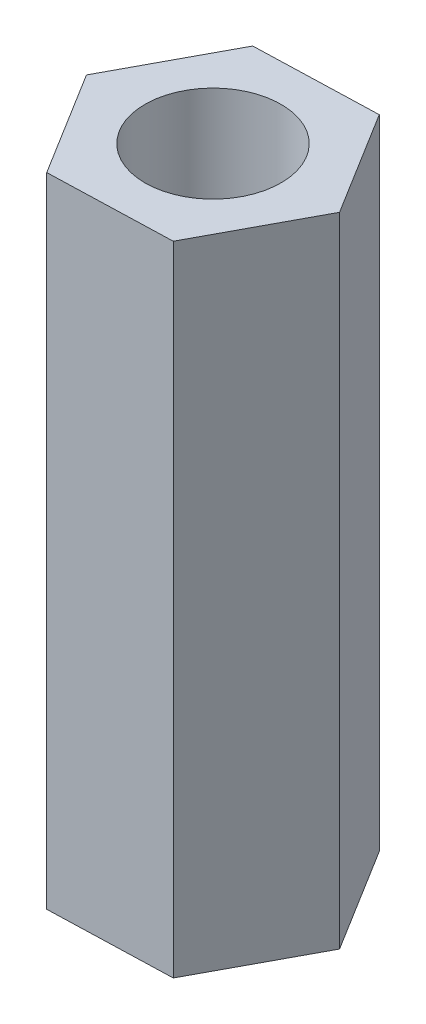
SolidWorks part; units mm, degrees
ref_plane "Front Plane" through (0, 0, 0) normal (0, 0, 1) x (1, 0, 0)
ref_plane "Top Plane" through (0, 0, 0) normal (0, 1, 0) x (1, 0, 0)
ref_plane "Right Plane" through (0, 0, 0) normal (1, 0, 0) x (0, 0, -1)
sketch "Sketch1" plane through (0, 0, 0) normal (0, 1, 0) x (1, 0, 0)
  line L1 (1.3651, 2.5436) -> (-1.5202, 2.454)
  line L2 (-1.5202, 2.454) -> (-2.8854, -0.0895)
  line L3 (-2.8854, -0.0895) -> (-1.3651, -2.5436)
  line L4 (-1.3651, -2.5436) -> (1.5202, -2.454)
  line L5 (1.5202, -2.454) -> (2.8854, 0.0895)
  line L6 (2.8854, 0.0895) -> (1.3651, 2.5436)
  circle A0 centre (0, 0) radius 1.6
  circle A1 centre (0, 0) radius 2.5 construction
extrude "Boss-Extrude1" add sketch "Sketch1" along normal blind 15
